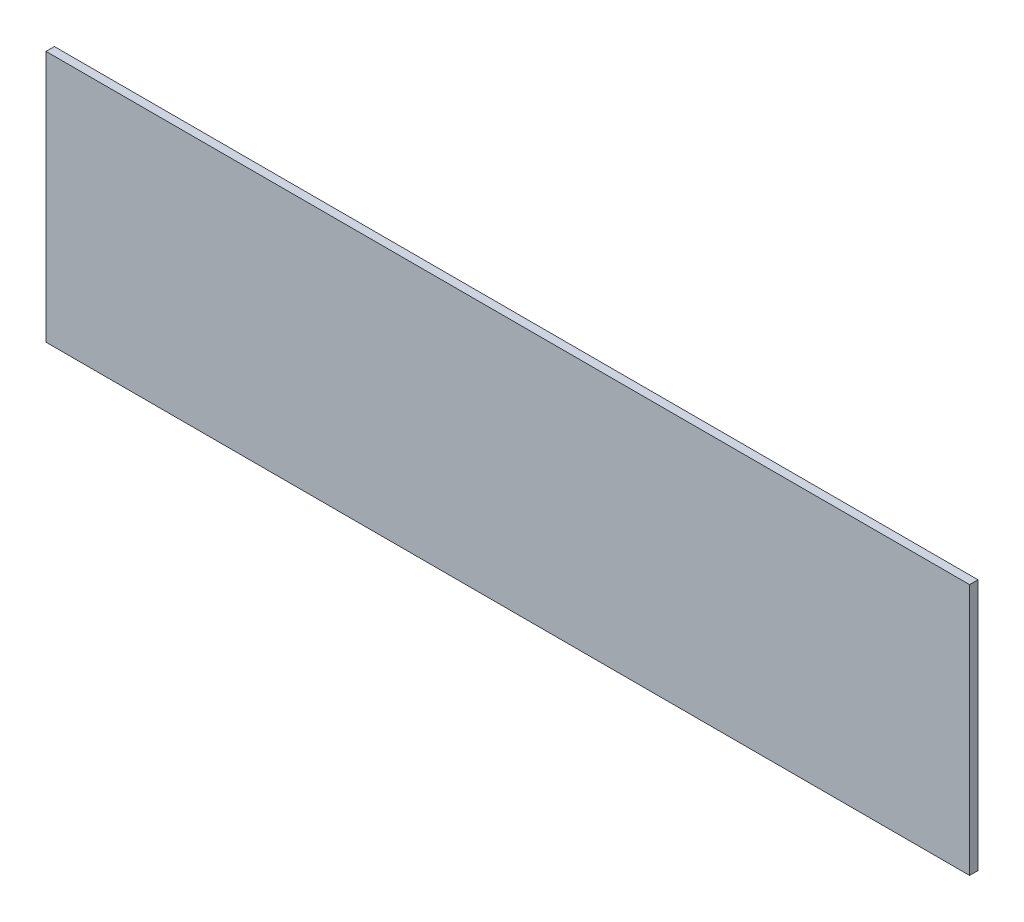
SolidWorks part; units mm, degrees
ref_plane "Front Plane" through (0, 0, 0) normal (0, 0, 1) x (1, 0, 0)
ref_plane "Top Plane" through (0, 0, 0) normal (0, 1, 0) x (1, 0, 0)
ref_plane "Right Plane" through (0, 0, 0) normal (1, 0, 0) x (0, 0, -1)
sketch "Sketch1" plane through (0, 0, 0) normal (0, 0, 1) x (1, 0, 0)
  line L1 (-275, 75) -> (275, 75)
  line L2 (-275, 75) -> (-275, -75)
  line L3 (-275, -75) -> (275, -75)
  line L4 (275, 75) -> (275, -75)
  line L5 (-275, 75) -> (275, -75) construction
  line L6 (-275, -75) -> (275, 75) construction
  point P0 (0, 0)
  dimension "D1" = 550
  dimension "D2" = 150
extrude "Boss-Extrude1" add sketch "Sketch1" along normal blind 5
